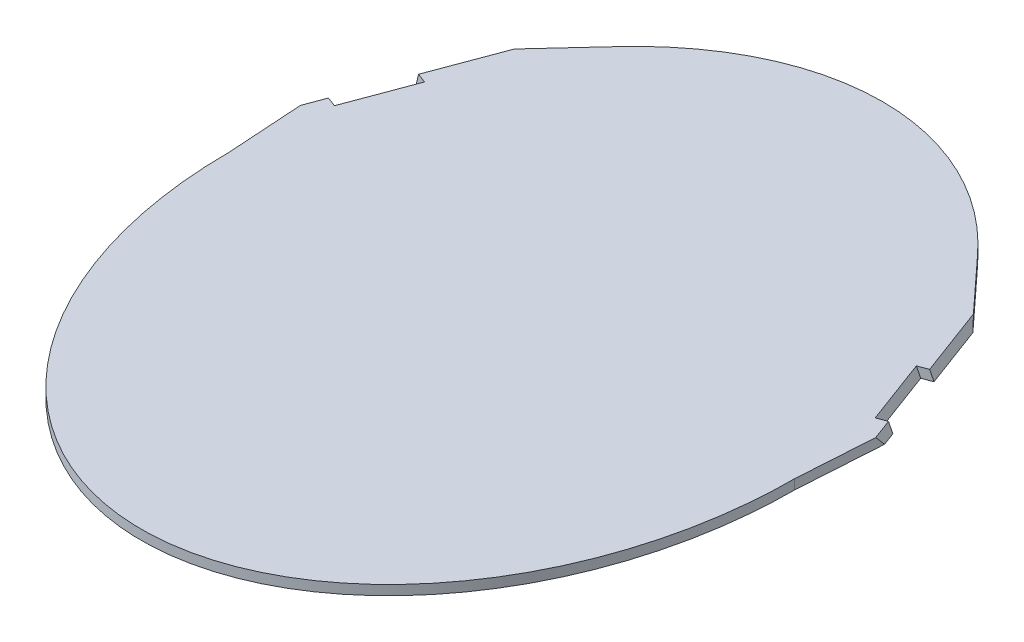
SolidWorks part; units mm, degrees
ref_plane "Front Plane" through (0, 0, 0) normal (0, 0, 1) x (1, 0, 0)
ref_plane "Top Plane" through (0, 0, 0) normal (0, 1, 0) x (1, 0, 0)
ref_plane "Right Plane" through (0, 0, 0) normal (1, 0, 0) x (0, 0, -1)
sketch "Sketch1" plane through (0, 0, 0) normal (0, 1, 0) x (1, 0, 0)
  ellipse E1 centre (0, 0) end of major axis (0, 380) minor radius 290
  dimension "D3" = 580
  dimension "D4" = 760
extrude "Boss-Extrude1" add sketch "Sketch1" along normal blind 10
sketch "Sketch2" plane through (0, 10, 0) normal (0, 1, 0) x (1, 0, 0)
  line L0 (287.228, 98.9933) -> (277.2296, 95.2629)
  line L1 (-296.5972, 102.489) -> (-290, 0)
  line L2 (277.2296, 95.2629) -> (290, 0)
  line L3 (244.7971, 227.7183) -> (188.9895, 288.2251)
  line L4 (262.12, 166.2887) -> (257.3363, 164.5039)
  line L5 (-287.228, 98.9933) -> (-296.5972, 102.489)
  line L6 (257.3363, 164.5039) -> (188.9895, 288.2251)
  line L7 (244.7971, 227.7183) -> (266.5349, 209.0252)
  line L8 (0, 0) -> (0, 519.0706) construction
  line L9 (-277.2296, 95.2629) -> (-290, 0)
  line L10 (-287.228, 98.9933) -> (-277.2296, 95.2629)
  line L11 (-266.5349, 209.0252) -> (-271.4892, 169.7843)
  line L12 (-262.12, 166.2887) -> (-271.4892, 169.7843)
  line L13 (-244.7971, 227.7183) -> (-266.5349, 209.0252)
  line L14 (-257.3363, 164.5039) -> (-188.9895, 288.2251)
  line L15 (275.9214, 98.9933) -> (250.8134, 166.2887) construction
  line L16 (287.228, 98.9933) -> (296.5972, 102.489)
  line L17 (296.5972, 102.489) -> (290, 0)
  line L18 (262.12, 166.2887) -> (271.4892, 169.7843)
  line L19 (266.5349, 209.0252) -> (271.4892, 169.7843)
  line L20 (-262.12, 166.2887) -> (-257.3363, 164.5039)
  line L21 (-244.7971, 227.7183) -> (-188.9895, 288.2251)
  ellipse E0 centre (0, 0) end of major axis (0, 380) minor radius 290 construction
  dimension "D1" = 10
  dimension "D2" = 10
extrude "Boss-Extrude2" add sketch "Sketch2" against normal blind 10
ref_plane "Plane1" through (256.4857, 95.6951, -95.6951) normal (0.8844, 0.33, -0.33) x (-0.3092, -0.1154, -0.944)
sketch "Sketch4" plane through (256.4857, 95.6951, -95.6951) normal (0.8844, 0.33, -0.33) x (-0.3092, -0.1154, -0.944)
  line L0 (4.6474, -100.4044) -> (0.9725, -70.5552)
  line L2 (0.9725, -70.5552) -> (72.261, -61.7784)
  line L3 (72.261, -61.7784) -> (74.7309, -81.8405)
  line L4 (74.7309, -81.8405) -> (75.9359, -91.6276)
  line L5 (75.9359, -91.6276) -> (4.6474, -100.4044)
  line L6 (3.8972, -94.3104) -> (3.2042, -88.6823) construction
extrude "Cut-Extrude1" cut sketch "Sketch4" against normal blind 10
mirror "Mirror1" about plane through (0, 0, 0) normal (1, 0, 0) of "Cut-Extrude1"
sketch "Sketch8" plane through (256.4857, 95.6951, -95.6951) normal (0.8844, 0.33, -0.33) x (-0.3092, -0.1154, -0.944)
  line L1 (-117.3026, 23.0684) -> (238.4926, 23.0684)
  line L2 (-117.3026, 23.0684) -> (-117.3026, -239.4472)
  line L3 (-117.3026, -239.4472) -> (238.4926, -239.4472)
  line L4 (238.4926, 23.0684) -> (238.4926, -239.4472)
extrude "Cut-Extrude2" cut sketch "Sketch8" along normal through all
mirror "Mirror2" about plane through (0, 0, 0) normal (1, 0, 0) of "Cut-Extrude2"
